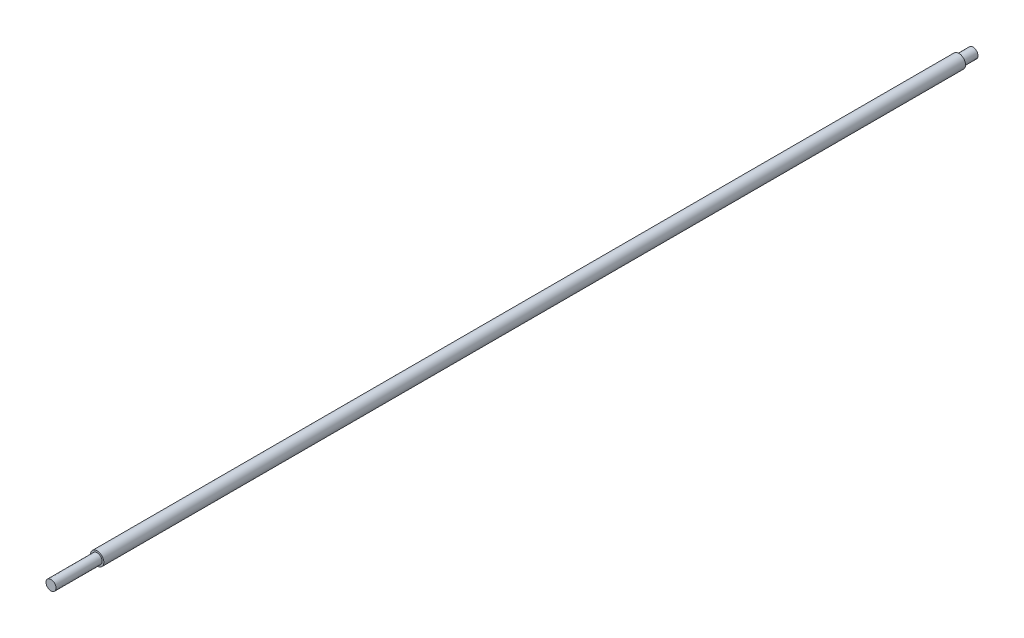
SolidWorks part; units mm, degrees
material "7079 Alloy"
ref_plane "Front" through (0, 0, 0) normal (0, 0, 1) x (1, 0, 0)
ref_plane "Top" through (0, 0, 0) normal (0, 1, 0) x (1, 0, 0)
ref_plane "Right" through (0, 0, 0) normal (1, 0, 0) x (0, 0, -1)
sketch "Sketch1" plane through (0, 0, 0) normal (0, 0, 1) x (1, 0, 0)
  circle A0 centre (0, 0) radius 8
extrude "Extrude1" add sketch "Sketch1" along normal blind 1102
sketch "Sketch3" plane through (0, 0, 1102) normal (0, 0, 1) x (1, 0, 0)
  circle A0 centre (0, 0) radius 6
  circle A1 centre (0, 0) radius 8
  circle M1 centre (0, 0) radius 8
extrude "Cut-Extrude1" cut sketch "Sketch3" against normal blind 54 contours A0 M1
sketch "Sketch4" plane through (0, 0, 0) normal (0, 0, -1) x (-1, 0, 0)
  circle A0 centre (0, 0) radius 6
  circle A1 centre (0, 0) radius 8
  circle M1 centre (0, 0) radius 8
extrude "Cut-Extrude2" cut sketch "Sketch4" against normal blind 20 contours A0 M1
sketch "Sketch5" plane through (0, 0, 1102) normal (0, 0, 1) x (1, 0, 0)
  circle A0 centre (0, 0) radius 6
extrude "Extrude2" add sketch "Sketch5" along normal blind 4.4
sketch "Sketch6" plane through (0, 0, 1048) normal (0, 0, 1) x (1, 0, 0)
  circle A0 centre (0, 0) radius 8
  circle A1 centre (0, 0) radius 6
extrude "Extrude3" add sketch "Sketch6" along normal blind 3
sketch "Sketch7" plane through (0, 0, 20) normal (0, 0, -1) x (-1, 0, 0)
  circle A0 centre (0, 0) radius 8
  circle A1 centre (0, 0) radius 6
extrude "Extrude4" add sketch "Sketch7" along normal blind 3
